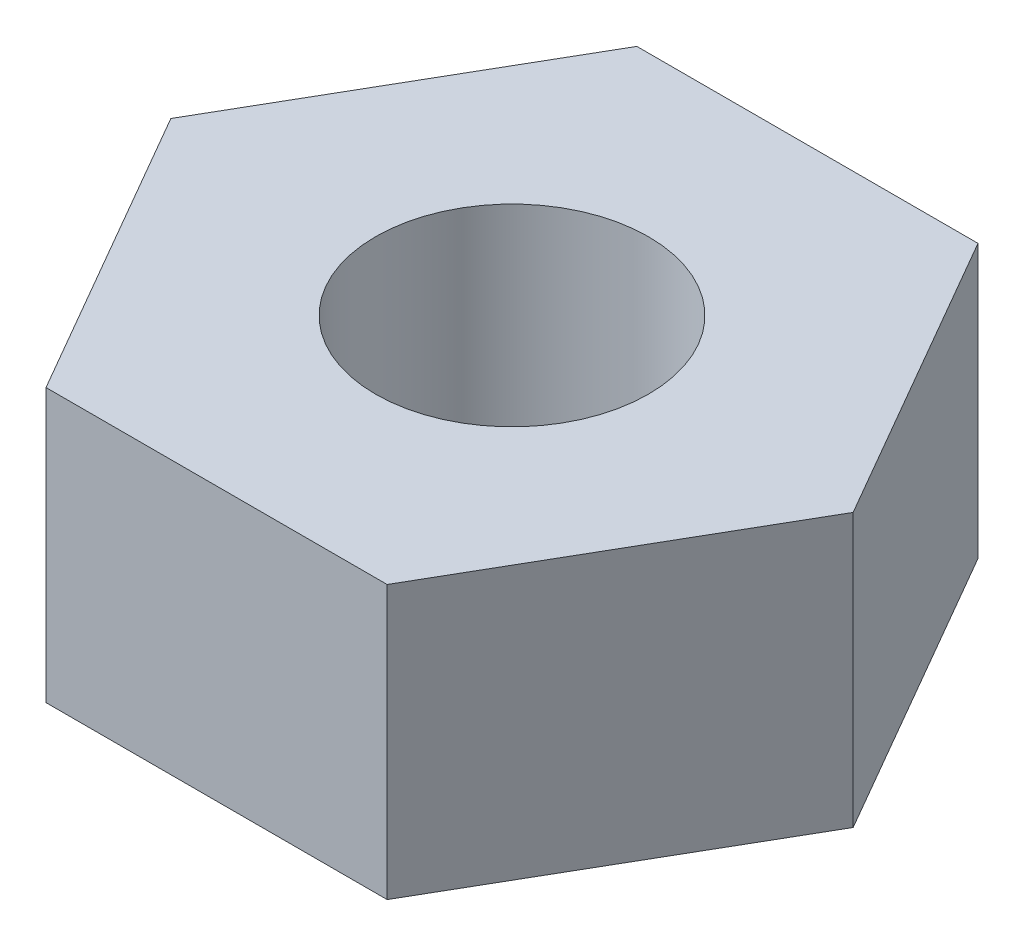
SolidWorks part; units mm, degrees
ref_plane "Alzado" through (0, 0, 0) normal (0, 0, 1) x (1, 0, 0)
ref_plane "Planta" through (0, 0, 0) normal (0, 1, 0) x (1, 0, 0)
ref_plane "Vista lateral" through (0, 0, 0) normal (1, 0, 0) x (0, 0, -1)
sketch "Croquis1" plane through (0, 0, 0) normal (0, 1, 0) x (1, 0, 0)
  line L1 (5, 0) -> (2.5, 4.3301)
  line L2 (2.5, 4.3301) -> (-2.5, 4.3301)
  line L3 (-2.5, 4.3301) -> (-5, 0)
  line L4 (-5, 0) -> (-2.5, -4.3301)
  line L5 (-2.5, -4.3301) -> (2.5, -4.3301)
  line L6 (2.5, -4.3301) -> (5, 0)
  circle A0 centre (0, 0) radius 4.3301 construction
  circle A1 centre (0, 0) radius 2
  dimension "D2" = 4
  dimension "D1" = 5
extrude "Saliente-Extruir1" add sketch "Croquis1" along normal blind 4
